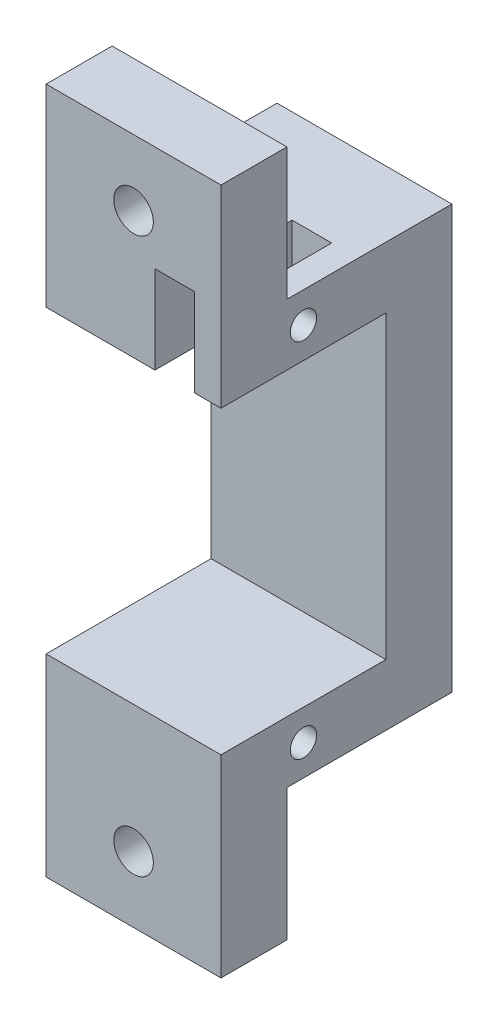
SolidWorks part; units mm, degrees
material "ABS"
ref_plane "Plano frontal" through (0, 0, 0) normal (0, 0, 1) x (1, 0, 0)
ref_plane "Plano superior" through (0, 0, 0) normal (0, 1, 0) x (1, 0, 0)
ref_plane "Plano direito" through (0, 0, 0) normal (1, 0, 0) x (0, 0, -1)
sketch "Esboço1" plane through (0, 0, 0) normal (0, 1, 0) x (1, 0, 0)
  line L1 (-21.7379, -6.1618) -> (-8.4879, -6.1618)
  line L2 (-21.7379, -6.1618) -> (-21.7379, -18.6618)
  line L3 (-21.7379, -18.6618) -> (-8.4879, -18.6618)
  line L4 (-8.4879, -6.1618) -> (-8.4879, -18.6618)
extrude "Ressalto-extrusão1" add sketch "Esboço1" against normal blind 4.65
sketch "Esboço2" plane through (0, 0, 6.1618) normal (0, 0, -1) x (-1, 0, 0)
  line L1 (21.7379, 0) -> (8.4879, 0)
  line L2 (21.7379, 0) -> (21.7379, -32.05)
  line L3 (21.7379, -32.05) -> (8.4879, -32.05)
  line L4 (8.4879, 0) -> (8.4879, -32.05)
extrude "Ressalto-extrusão2" add sketch "Esboço2" along normal blind 5
sketch "Esboço3" plane through (0, 0, 6.1618) normal (0, 0, 1) x (1, 0, 0)
  line L0 (-21.7379, -32.05) -> (-21.7379, -4.65) construction
  line L1 (-8.4879, -32.05) -> (-21.7379, -32.05)
  line L2 (-8.4879, -32.05) -> (-8.4879, -27.4)
  line L3 (-8.4879, -27.4) -> (-21.7379, -27.4)
  line L4 (-21.7379, -32.05) -> (-21.7379, -27.4)
extrude "Ressalto-extrusão3" add sketch "Esboço3" along normal blind 12.5
sketch "Esboço4" plane through (0, -32.05, 0) normal (0, -1, 0) x (-1, 0, 0)
  line L0 (8.4879, -1.1618) -> (8.4879, -18.6618) construction
  line L1 (21.7379, -18.6618) -> (8.4879, -18.6618)
  line L2 (21.7379, -18.6618) -> (21.7379, -13.6618)
  line L3 (21.7379, -13.6618) -> (8.4879, -13.6618)
  line L4 (8.4879, -18.6618) -> (8.4879, -13.6618)
extrude "Ressalto-extrusão4" add sketch "Esboço4" along normal blind 10
sketch "Esboço5" plane through (0, 0, 0) normal (0, 1, 0) x (1, 0, 0)
  line L0 (-8.4879, -18.6618) -> (-8.4879, -1.1618) construction
  line L1 (-21.7379, -18.6618) -> (-8.4879, -18.6618)
  line L2 (-21.7379, -18.6618) -> (-21.7379, -13.6618)
  line L3 (-21.7379, -13.6618) -> (-8.4879, -13.6618)
  line L4 (-8.4879, -18.6618) -> (-8.4879, -13.6618)
extrude "Ressalto-extrusão5" add sketch "Esboço5" along normal blind 10
sketch "Esboço6" plane through (0, 0, 13.6618) normal (0, 0, -1) x (-1, 0, 0)
  line L0 (8.4879, 10) -> (21.7379, 10) construction
  line L1 (21.7379, 10) -> (21.7379, 0) construction
  line L2 (21.7379, -42.05) -> (8.4879, -42.05) construction
  line L3 (21.7379, -42.05) -> (21.7379, -32.05) construction
  circle A0 centre (15.1129, 5) radius 1.5
  circle A1 centre (15.1129, -37.05) radius 1.5
  point P10 (15.1129, -42.05)
  point P13 (21.7379, -37.05)
  dimension "D1" = 5
  dimension "D2" = 6.625
  dimension "D3" = 5
  dimension "D4" = 6.625
extrude "Corte-extrusão1" cut sketch "Esboço6" against normal blind 10
sketch "Esboço7" plane through (-8.4879, 0, 0) normal (1, 0, 0) x (0, 0, -1)
  line L0 (-18.6618, -4.65) -> (-18.6618, 10) construction
  line L1 (-13.6618, 0) -> (-1.1618, 0) construction
  circle A0 centre (-12.4118, -2.325) radius 1
  dimension "D1" = 6.25
  dimension "D2" = 2.325
sketch "Esboço8" plane through (-8.4879, 0, 0) normal (1, 0, 0) x (0, 0, -1)
  line L0 (-18.6618, -42.05) -> (-18.6618, -27.4) construction
  line L1 (-1.1618, -32.05) -> (-13.6618, -32.05) construction
  circle A0 centre (-12.4118, -29.725) radius 1
  dimension "D1" = 6.25
  dimension "D2" = 2.325
extrude "Corte-extrusão2" cut sketch "Esboço7" against normal through all
extrude "Corte-extrusão3" cut sketch "Esboço8" against normal through all
sketch "Esboço9" plane through (0, 0, 0) normal (0, 1, 0) x (1, 0, 0)
  line L0 (-8.4879, -13.6618) -> (-8.4879, -1.1618) construction
  line L1 (-13.4879, -18.6618) -> (-10.4879, -18.6618)
  line L2 (-13.4879, -18.6618) -> (-13.4879, -8.2708)
  line L3 (-13.4879, -8.2708) -> (-10.4879, -8.2708)
  line L4 (-10.4879, -18.6618) -> (-10.4879, -8.2708)
  line L7 (-21.7379, -18.6618) -> (-8.4879, -18.6618) construction
  dimension "D1" = 2
  dimension "D2" = 3
  dimension "D3" = 0
extrude "Corte-extrusão4" cut sketch "Esboço9" against normal blind 10
sketch "Esboço10" plane through (0, 0, 13.6618) normal (0, 0, -1) x (-1, 0, 0)
  line L0 (8.4879, 0) -> (10.4879, 0) construction
  line L1 (10.4879, 0) -> (13.4879, 0)
  line L2 (10.4879, 0) -> (10.4879, 2)
  line L3 (10.4879, 2) -> (13.4879, 2)
  line L4 (13.4879, 0) -> (13.4879, 2)
  line L5 (8.4879, 10) -> (8.4879, 0) construction
  dimension "D1" = 2
extrude "Corte-extrusão5" cut sketch "Esboço10" against normal blind 10
